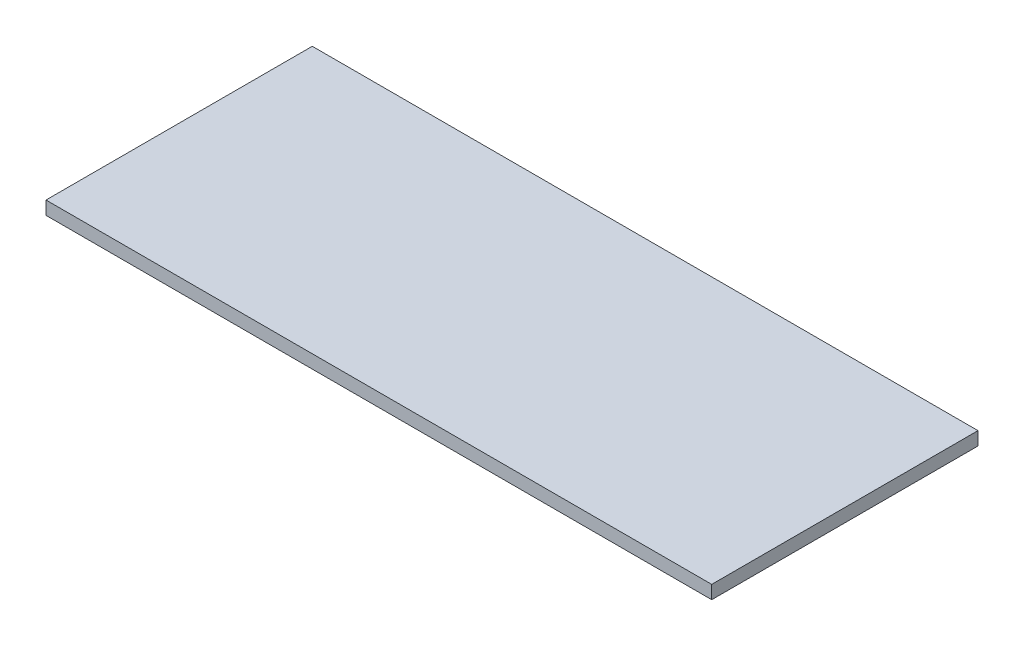
SolidWorks part; units mm, degrees
ref_plane "Front Plane" through (0, 0, 0) normal (0, 0, 1) x (1, 0, 0)
ref_plane "Top Plane" through (0, 0, 0) normal (0, 1, 0) x (1, 0, 0)
ref_plane "Right Plane" through (0, 0, 0) normal (1, 0, 0) x (0, 0, -1)
sketch "Sketch1" plane through (0, 0, 0) normal (0, 1, 0) x (1, 0, 0)
  line L1 (-100, -40) -> (100, -40)
  line L2 (-100, -40) -> (-100, 40)
  line L3 (-100, 40) -> (100, 40)
  line L4 (100, -40) -> (100, 40)
  line L5 (-100, -40) -> (100, 40) construction
  line L6 (-100, 40) -> (100, -40) construction
  point P0 (0, 0)
  dimension "D1" = 200
  dimension "D2" = 80
extrude "Boss-Extrude1" add sketch "Sketch1" along normal blind 4
